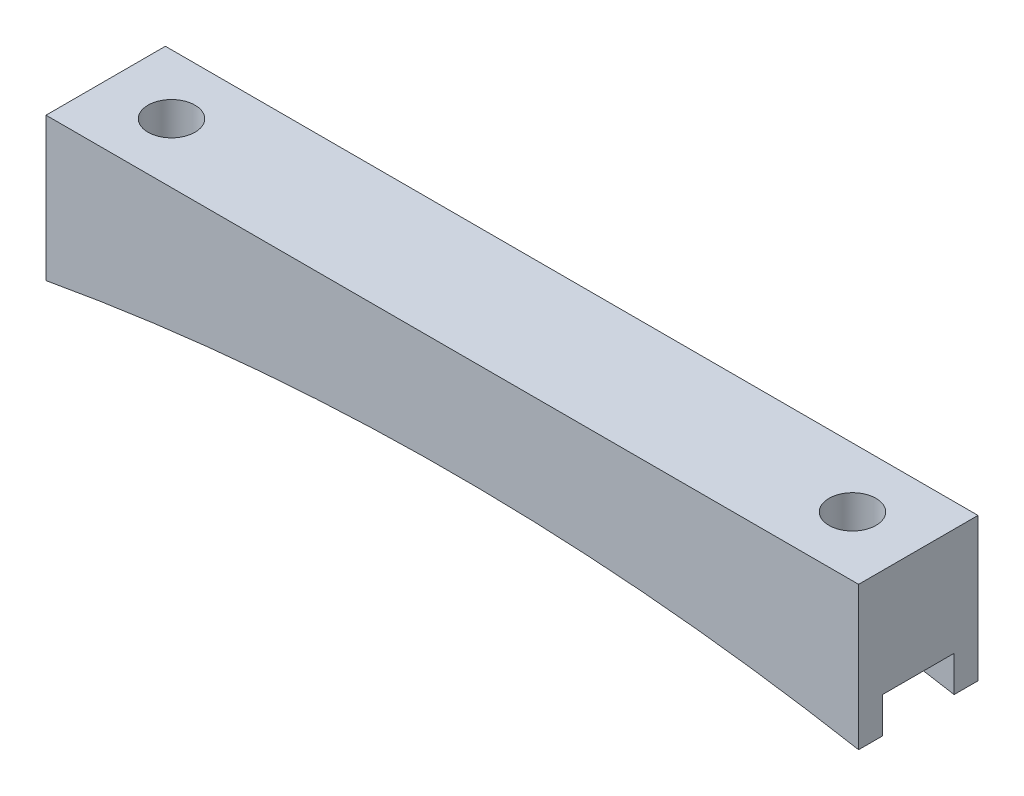
SolidWorks part; units mm, degrees
ref_plane "Front Plane" through (0, 0, 0) normal (0, 0, 1) x (1, 0, 0)
ref_plane "Top Plane" through (0, 0, 0) normal (0, 1, 0) x (1, 0, 0)
ref_plane "Right Plane" through (0, 0, 0) normal (1, 0, 0) x (0, 0, -1)
sketch "Sketch1" plane through (0, 0, 0) normal (0, 0, 1) x (1, 0, 0)
  line L0 (-43.22, 0) -> (43.22, 0)
  line L1 (-36.22, -2.54) -> (36.22, -2.54) construction
  line L2 (0, 0) -> (0, -4.6068) construction
  line L3 (43.22, 0) -> (43.22, -15.24)
  line L4 (-43.22, 0) -> (-43.22, -15.24)
  arc A0 (-43.22, -15.24) -> (43.22, -15.24) centre (0, -252.6378) cw
  point P4 (0, 0)
  point P9 (0, -2.54)
  dimension "D4" = 241.3
  dimension "D1" = 72.44
  dimension "D2" = 2.54
  dimension "D3" = 7
  dimension "D5" = 15.24
extrude "Boss-Extrude1" add sketch "Sketch1" along normal blind 12.7
sketch "Sketch2" plane through (0, 0, 0) normal (0, 1, 0) x (1, 0, 0)
  line L1 (-36.22, 0) -> (-36.22, -12.7) construction
  line L2 (-43.22, 0) -> (43.22, 0) construction
  line L3 (43.22, -12.7) -> (-43.22, -12.7) construction
  line L4 (36.22, 0) -> (36.22, -12.7) construction
  circle A0 centre (-36.22, -6.35) radius 2.5
  circle A1 centre (36.22, -6.35) radius 2.5
  circle A2 centre (-36.22, -6.35) radius 3 construction
  point P7 (-36.22, -6.35)
  dimension "D1" = 5
  dimension "D2" = 6
extrude "Cut-Extrude1" cut sketch "Sketch2" against normal through all
sketch "Sketch3" plane through (43.22, 0, 0) normal (1, 0, 0) x (0, 0, -1)
  line L0 (-12.7, -15.24) -> (0, -15.24) construction
  line L1 (-10.16, -15.24) -> (-2.54, -15.24)
  line L2 (-10.16, -15.24) -> (-10.16, -11.43)
  line L3 (-10.16, -11.43) -> (-2.54, -11.43)
  line L4 (-2.54, -15.24) -> (-2.54, -11.43)
  line L5 (-12.7, -15.24) -> (-12.7, 0) construction
  line L6 (0, -15.24) -> (0, 0) construction
  dimension "D1" = 2.54
  dimension "D2" = 2.54
  dimension "D3" = 3.81
extrude "Cut-Extrude2" cut sketch "Sketch3" against normal through all
